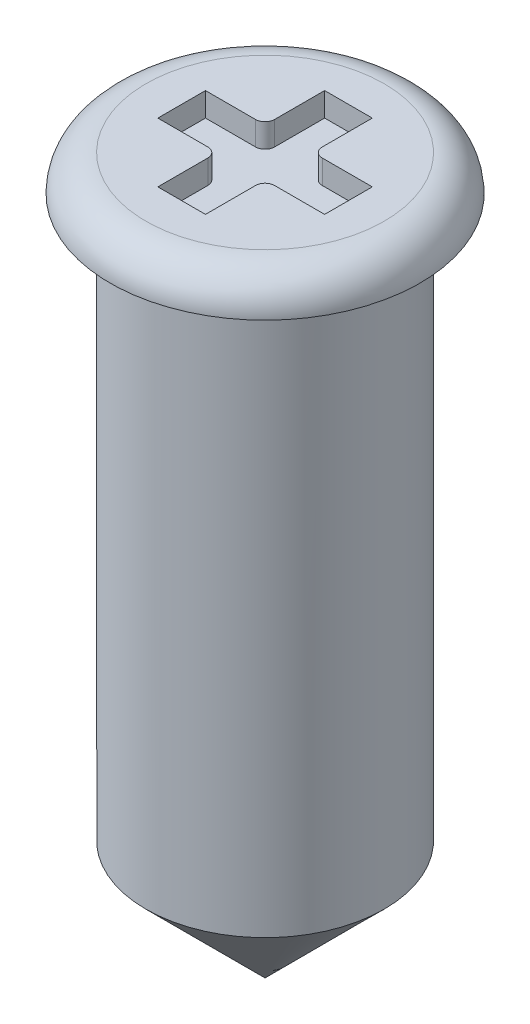
SolidWorks part; units mm, degrees
ref_plane "Front" through (0, 0, 0) normal (0, 0, 1) x (1, 0, 0)
ref_plane "Top" through (0, 0, 0) normal (0, 1, 0) x (1, 0, 0)
ref_plane "Right" through (0, 0, 0) normal (1, 0, 0) x (0, 0, -1)
sketch "Sketch1" plane through (0, 0, 0) normal (0, 0, 1) x (1, 0, 0)
  line L0 (0, -19.516) -> (0.5, -19.516)
  line L1 (0, -55) -> (0, 55) construction
  line L2 (0.5, -19.816) -> (0.5, -22.016)
  line L4 (0, -22.516) -> (0, -19.516)
  line L5 (0.65, -19.666) -> (0.5, -19.666)
  line L6 (0.5, -19.816) -> (0.5, -19.666)
  line L7 (0, -22.516) -> (0.5, -22.016)
  arc A0 (0.65, -19.666) -> (0.5, -19.516) centre (0.5, -19.666) ccw
  point P8 (0.5, -19.516)
  point P10 (0.5, -19.516)
  dimension "D3" = 0.3
revolve "Revolve1" add sketch "Sketch1" angle 360 about L4
cosmetic thread "Cosmetic Thread1" parameters "D2"=0.1
sketch "Sketch2" plane through (0, -19.516, 0) normal (0, 1, 0) x (1, 0, 0)
  line L0 (-0.1, 0.35) -> (0.1, 0.35)
  line L1 (0, -0.715) -> (0, 0.715) construction
  line L2 (0.1, 0.35) -> (0.1, 0.14)
  line L3 (0.14, 0.1) -> (0.35, 0.1)
  line L4 (0.35, 0.1) -> (0.35, -0.1)
  line L5 (0.35, -0.1) -> (0.14, -0.1)
  line L6 (0.1, -0.14) -> (0.1, -0.35)
  line L7 (0.1, -0.35) -> (-0.1, -0.35)
  line L8 (-0.715, 0) -> (0.715, 0) construction
  line L9 (0, 0.35) -> (0, -0.35) construction
  line L10 (-0.1, -0.14) -> (-0.1, -0.35)
  line L11 (-0.35, -0.1) -> (-0.14, -0.1)
  line L12 (-0.35, 0.1) -> (-0.35, -0.1)
  line L13 (-0.14, 0.1) -> (-0.35, 0.1)
  line L14 (-0.1, 0.35) -> (-0.1, 0.14)
  arc A0 (0.1, 0.14) -> (0.14, 0.1) centre (0.14, 0.14) ccw
  arc A1 (0.14, -0.1) -> (0.1, -0.14) centre (0.14, -0.14) ccw
  arc A2 (-0.14, -0.1) -> (-0.1, -0.14) centre (-0.14, -0.14) cw
  arc A3 (-0.1, 0.14) -> (-0.14, 0.1) centre (-0.14, 0.14) cw
  point P14 (0.1, 0.1)
  point P17 (0.1, -0.1)
  dimension "D8" = 0.04
  dimension "D9" = 0.04
  dimension "D1" = 0.2
  dimension "D2" = 0.25
  dimension "D3" = 0.25
  dimension "D4" = 0.25
  dimension "D5" = 0.25
  dimension "D6" = 0.1
  dimension "D7" = 0.1
extrude "Cut-Extrude1" cut sketch "Sketch2" against normal blind 0.1
